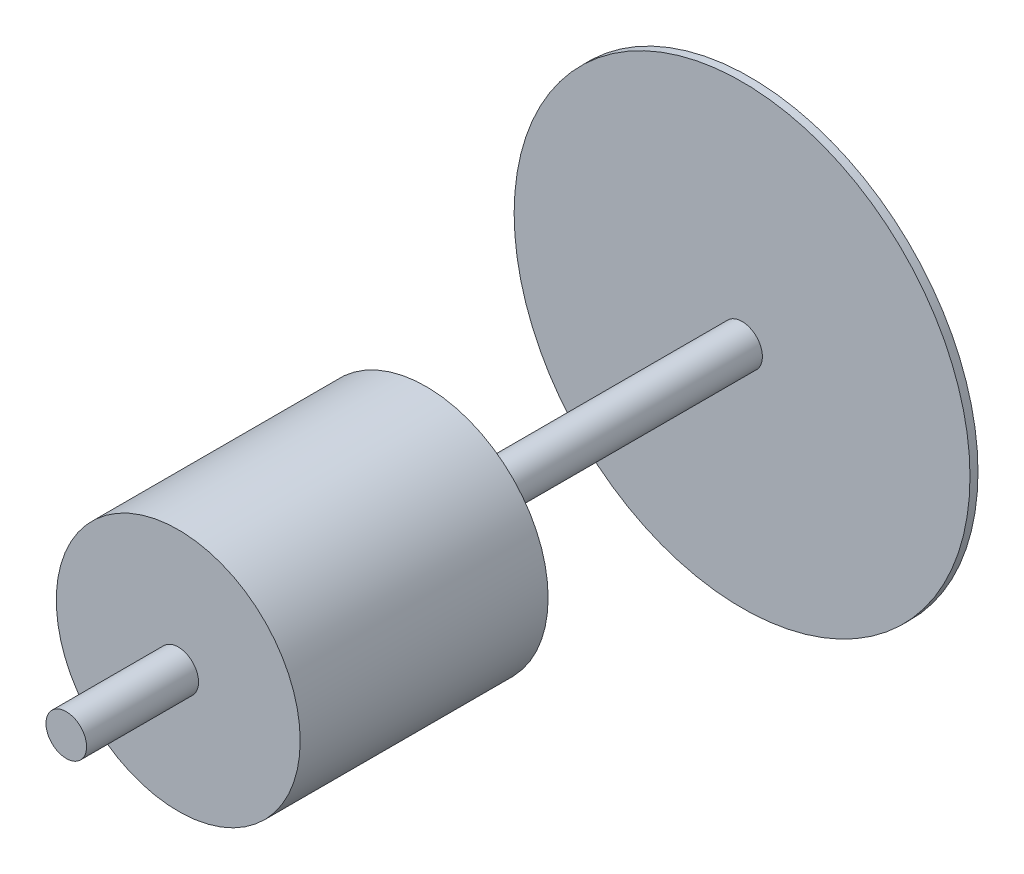
SolidWorks part; units mm, degrees
other "Markup1"
sketch "Sketch6" plane through (500, -500, -1363.6) normal (1, 0, 0) x (0, 0, -1)
ref_plane "Top Plane" through (0, 0, 0) normal (0, 0, 1) x (1, 0, 0)
ref_plane "Right Plane" through (0, 0, 0) normal (0, 1, 0) x (1, 0, 0)
ref_plane "Front Plane" through (0, 0, 0) normal (1, 0, 0) x (0, 0, -1)
sketch "Sketch1" plane through (0, 0, 0) normal (0, 0, 1) x (1, 0, 0)
  circle A0 centre (0, 0) radius 50.8
  dimension "D1" = 101.6
extrude "Boss-Extrude1" add sketch "Sketch1" against normal blind 680 and the other way blind 1030
sketch "Sketch2" plane through (0, 0, -680) normal (0, 0, 1) x (1, 0, 0)
  circle A0 centre (0, 0) radius 570
  dimension "D1" = 1140
extrude "Boss-Extrude2" add sketch "Sketch2" along normal blind 20
sketch "Sketch3" plane through (0, 0, -660) normal (0, 0, 1) x (1, 0, 0)
  circle A0 centre (0, 0) radius 222.25
  dimension "D1" = 444.5
sketch "Sketch7" plane through (0, 0, 1030) normal (0, 0, 1) x (1, 0, 0)
  circle A0 centre (0, 0) radius 305
extrude "Boss-Extrude3" add sketch "Sketch7" along a picked direction on the side against the normal blind 620 from offset 280 offset against normal yes
sketch "Sketch8" plane through (0, 0, 130) normal (0, 0, -1) x (-1, 0, 0)
  circle A0 centre (0, 0) radius 225
extrude "Boss-Extrude4" add sketch "Sketch8" along normal blind 50
